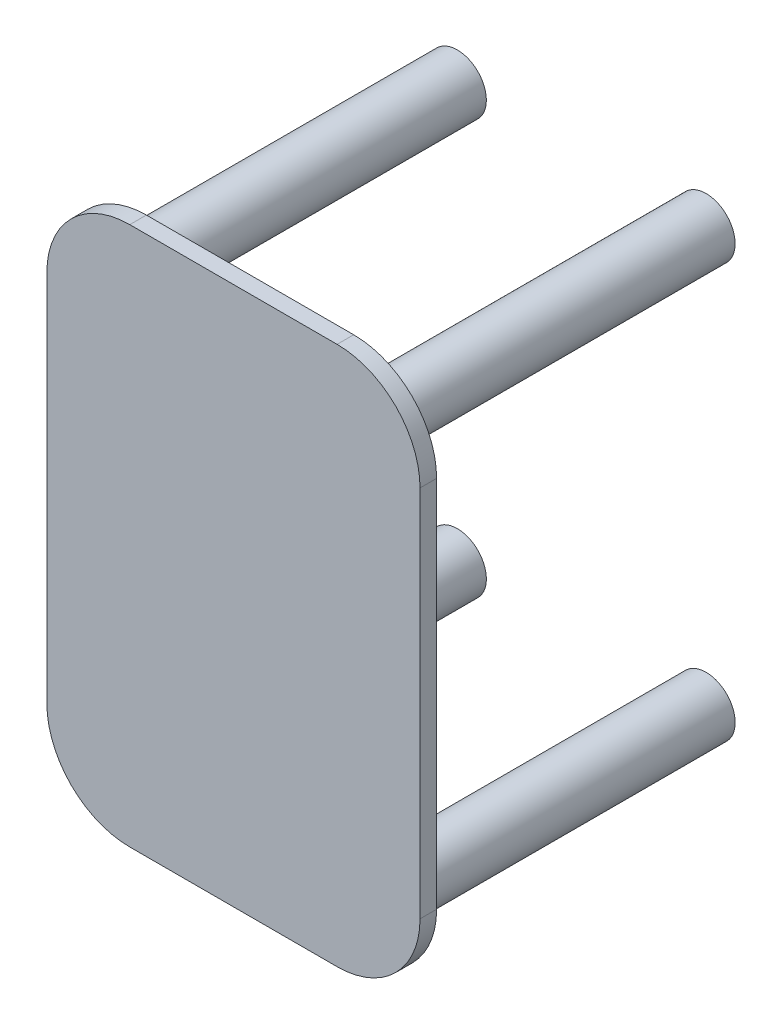
SolidWorks part; units mm, degrees
ref_plane "Front Plane" through (0, 0, 0) normal (0, 0, 1) x (1, 0, 0)
ref_plane "Top Plane" through (0, 0, 0) normal (0, 1, 0) x (1, 0, 0)
ref_plane "Right Plane" through (0, 0, 0) normal (1, 0, 0) x (0, 0, -1)
sketch "Sketch1" plane through (0, 0, 0) normal (0, 0, 1) x (1, 0, 0)
  line L0 (0, 0.25) -> (0, -0.25) construction
  line L1 (-0.15, -0.25) -> (0.15, -0.25) construction
  line L2 (-0.15, -0.25) -> (-0.15, 0.25) construction
  line L3 (-0.15, 0.25) -> (0.15, 0.25) construction
  line L4 (0.15, -0.25) -> (0.15, 0.25) construction
  line L5 (-0.15, -0.25) -> (0.15, 0.25) construction
  line L6 (-0.15, 0.25) -> (0.15, -0.25) construction
  line L7 (-0.15, 0) -> (0.15, 0) construction
  circle A0 centre (-0.15, 0.25) radius 0.035
  circle A1 centre (-0.15, -0.25) radius 0.035
  circle A2 centre (0.15, -0.25) radius 0.035
  circle A3 centre (0.15, 0.25) radius 0.035
  point P0 (0, 0)
  dimension "D3" = 0.07
  dimension "D1" = 0.3
  dimension "D2" = 0.5
extrude "Boss-Extrude1" add sketch "Sketch1" along normal blind 0.4
ref_plane "Plane1" through (0, 0, 0.4) normal (0, 0, 1) x (1, 0, 0)
sketch "Sketch2" plane through (0, 0, 0.4) normal (0, 0, 1) x (1, 0, 0)
  line L1 (-0.125, -0.325) -> (0.125, -0.325)
  line L2 (-0.225, -0.225) -> (-0.225, 0.225)
  line L3 (-0.125, 0.325) -> (0.125, 0.325)
  line L4 (0.225, -0.225) -> (0.225, 0.225)
  line L5 (-0.225, -0.325) -> (0.225, 0.325) construction
  line L6 (-0.225, 0.325) -> (0.225, -0.325) construction
  arc A0 (-0.225, -0.225) -> (-0.125, -0.325) centre (-0.125, -0.225) ccw
  arc A1 (0.125, -0.325) -> (0.225, -0.225) centre (0.125, -0.225) ccw
  arc A2 (0.225, 0.225) -> (0.125, 0.325) centre (0.125, 0.225) ccw
  arc A3 (-0.125, 0.325) -> (-0.225, 0.225) centre (-0.125, 0.225) ccw
  point P0 (0, 0)
  dimension "D3" = 0.1
  dimension "D1" = 0.65
  dimension "D2" = 0.45
extrude "Boss-Extrude2" add sketch "Sketch2" along normal blind 0.02 separate body
